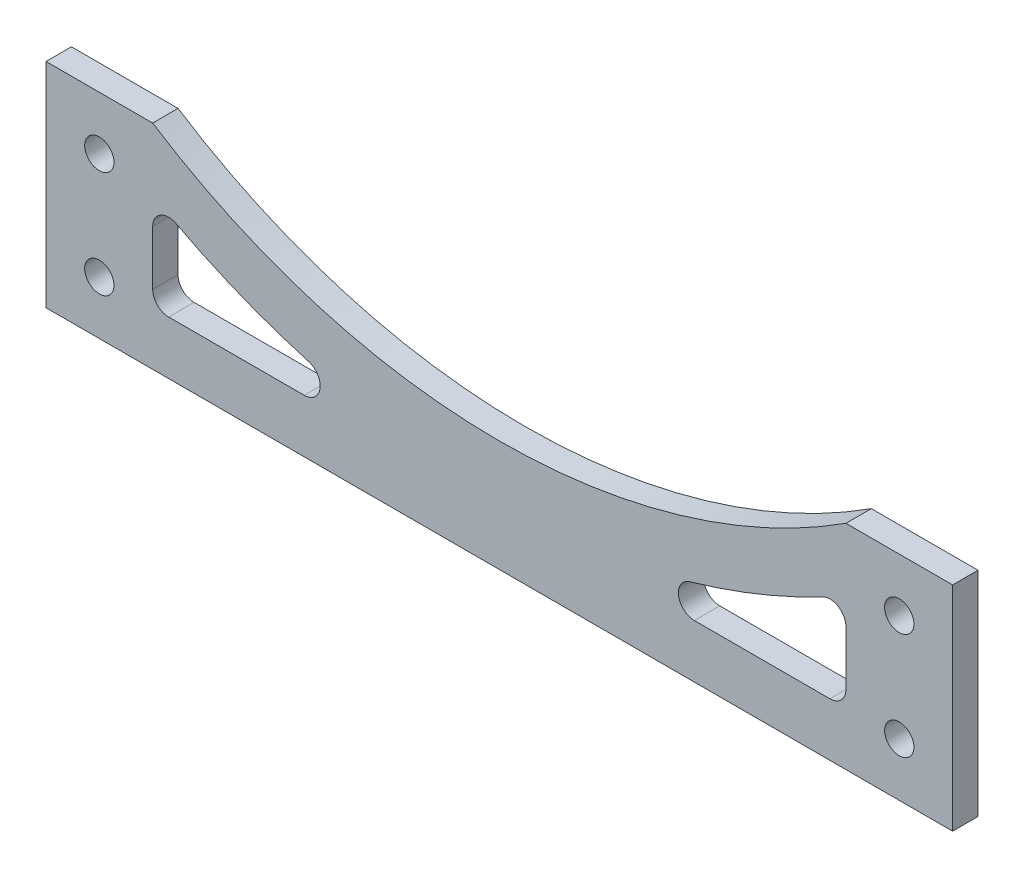
SolidWorks part; units mm, degrees
ref_plane "Front Plane" through (0, 0, 0) normal (0, 0, 1) x (1, 0, 0)
ref_plane "Top Plane" through (0, 0, 0) normal (0, 1, 0) x (1, 0, 0)
ref_plane "Right Plane" through (0, 0, 0) normal (1, 0, 0) x (0, 0, -1)
sketch "Sketch1" plane through (0, 0, 0) normal (0, 0, 1) x (1, 0, 0)
  line L0 (-85, 0) -> (85, 0)
  line L1 (85, 0) -> (85, 40)
  line L2 (85, 40) -> (65, 40)
  line L3 (-85, 0) -> (-85, 40)
  line L4 (-85, 40) -> (-65, 40)
  line L5 (-75, 40) -> (-75, 30) construction
  line L6 (75, 40) -> (75, 30) construction
  line L7 (-65, 23.2064) -> (-65, 13)
  line L8 (-62, 10) -> (-36.5781, 10)
  line L9 (65, 23.2064) -> (65, 13)
  line L10 (62, 10) -> (36.5781, 10)
  arc A1 (-65, 40) -> (65, 40) centre (0, 140.8712) ccw
  circle A2 centre (-75, 30) radius 2.75
  circle A3 centre (-75, 10) radius 2.75
  circle A4 centre (75, 30) radius 2.75
  circle A5 centre (75, 10) radius 2.75
  arc A6 (-60.6015, 25.8605) -> (-35.753, 15.8843) centre (0, 140.8712) ccw
  arc A7 (-36.5781, 10) -> (-35.753, 15.8843) centre (-36.5781, 13) ccw
  arc A8 (35.753, 15.8843) -> (36.5781, 10) centre (36.5781, 13) ccw
  arc A9 (-70.4167, 31.5941) -> (70.4167, 31.5941) centre (0, 140.8712) ccw construction
  arc A10 (65, 23.2064) -> (60.6015, 25.8605) centre (62, 23.2064) ccw
  arc A11 (65, 13) -> (62, 10) centre (62, 13) cw
  arc A12 (-65, 13) -> (-62, 10) centre (-62, 13) ccw
  arc A13 (-60.6015, 25.8605) -> (-65, 23.2064) centre (-62, 23.2064) ccw
  arc A14 (35.753, 15.8843) -> (60.6015, 25.8605) centre (0, 140.8712) ccw
  dimension "D6" = 120
  dimension "D7" = 5.5
  dimension "D12" = 6
  dimension "D13" = 3
  dimension "D1" = 40
  dimension "D2" = 20
  dimension "D4" = 170
  dimension "D8" = 10
  dimension "D9" = 10
  dimension "D11" = 10
  dimension "D10" = 10
extrude "Boss-Extrude1" add sketch "Sketch1" along normal blind 4.7625
